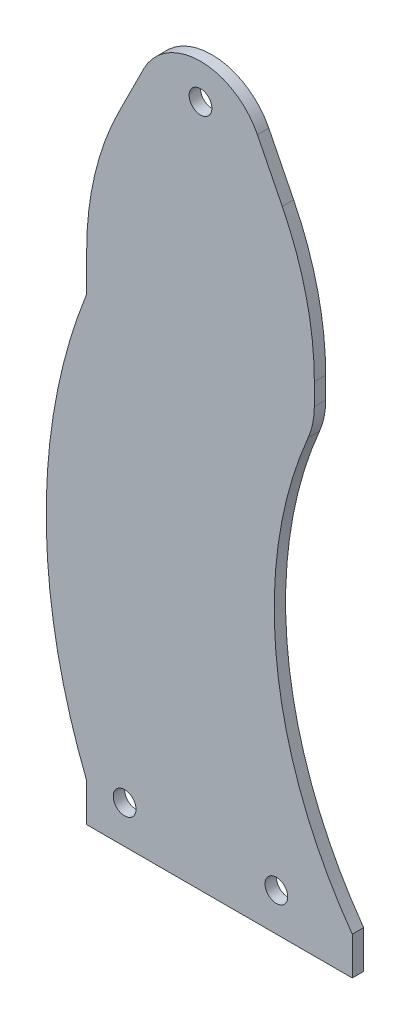
SolidWorks part; units mm, degrees
material "普通碳钢"
ref_plane "前视基准面" through (0, 0, 0) normal (0, 0, 1) x (1, 0, 0)
ref_plane "上视基准面" through (0, 0, 0) normal (0, 1, 0) x (1, 0, 0)
ref_plane "右视基准面" through (0, 0, 0) normal (1, 0, 0) x (0, 0, -1)
sketch "草图1" plane through (0, 0, 0) normal (0, 0, 1) x (1, 0, 0)
  line L0 (8.4458, 166.8916) -> (15, 180)
  line L1 (30, 180) -> (30, 0) construction
  line L2 (15, 180) -> (45, 180) construction
  line L3 (0, 131.1146) -> (0, 121.1146)
  line L4 (0, 0) -> (60, 0)
  line L5 (60, 131.1146) -> (60, 125.4124)
  line L6 (51.5542, 166.8916) -> (45, 180)
  line L7 (60, 0) -> (70, 0)
  line L8 (70, 0) -> (70, 10)
  line L9 (0, 10) -> (0, 0)
  line L10 (50, 10) -> (80, 10) construction
  line L11 (80, 10) -> (80, 107.6571) construction
  line L12 (58.3732, 117.5113) -> (43.1172, 82.0353) construction
  line L13 (58.3732, 117.5113) -> (91.6973, 103.1808) construction
  line L14 (49.4255, 74.0553) -> (49.4255, 31.988) construction
  line L15 (49.4255, 74.0553) -> (120.2204, 74.0553) construction
  arc A0 (60, 131.1146) -> (51.5542, 166.8916) centre (-20, 131.1146) ccw
  arc A1 (0, 131.1146) -> (8.4458, 166.8916) centre (80, 131.1146) cw
  arc A2 (15, 180) -> (45, 180) centre (30, 172.5) cw
  arc A3 (70, 10) -> (58.3732, 117.5113) centre (159.4255, 74.0553) cw
  arc A4 (58.3732, 117.5113) -> (60, 125.4124) centre (40, 125.4124) ccw
  circle A5 centre (10, 10) radius 3
  circle A6 centre (50, 10) radius 3
  circle A7 centre (30, 180) radius 3
  arc A9 (0, 10) -> (0, 121.1146) centre (139.3319, 65.5573) cw
  point P13 (60, 150)
  point P16 (0, 150)
  point P22 (60, 121.1146)
  dimension "D5" = 80
  dimension "D6" = 80
  dimension "D7" = 10
  dimension "D8" = 10
  dimension "D10" = 110
  dimension "D11" = 20
  dimension "D12" = 6
  dimension "D15" = 6
  dimension "D17" = 10
  dimension "D19" = 150
  dimension "D1" = 30
  dimension "D2" = 60
  dimension "D3" = 15
  dimension "D4" = 180
  dimension "D9" = 10
  dimension "D13" = 10
  dimension "D14" = 10
  dimension "D16" = 0
  dimension "D18" = 10
  dimension "D20" = 10
  dimension "D21" = 90.2223
  dimension "D22" = 64.0553
extrude "凸台-拉伸1" add sketch "草图1" along normal blind 3
